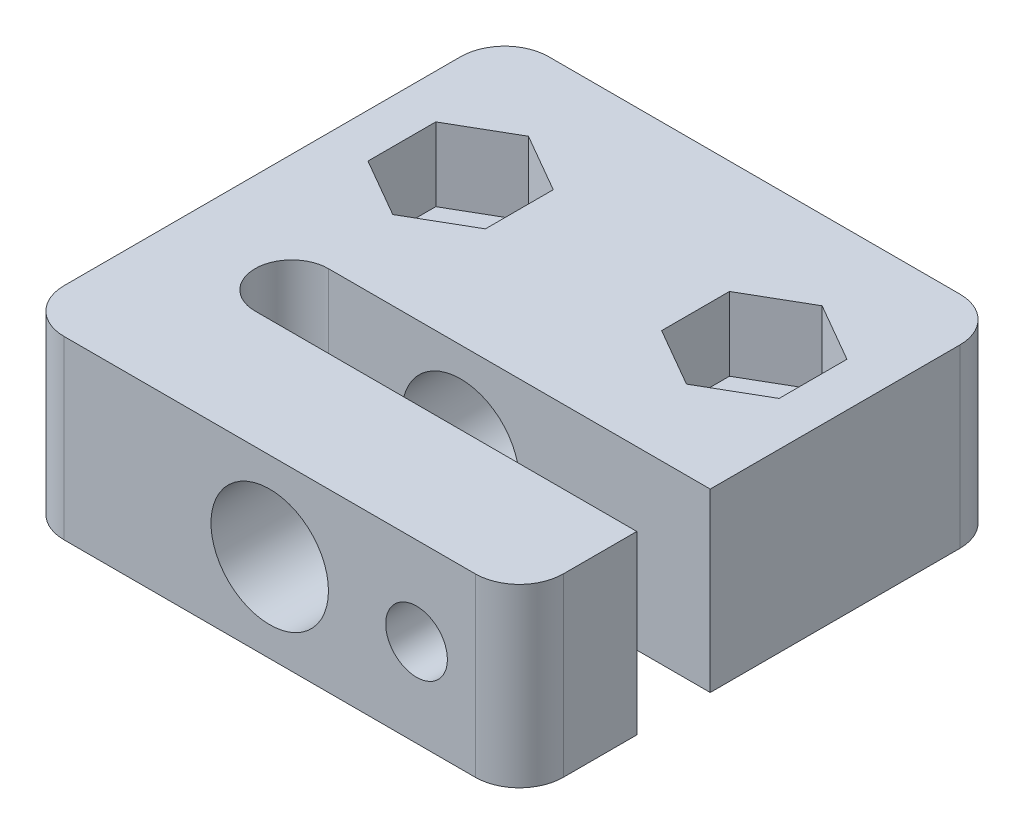
SolidWorks part; units mm, degrees
material "Delrin 2700 NC010, Low Viscosity Acetal Copolymer (SS)"
ref_plane "Front Plane" through (0, 0, 0) normal (0, 0, 1) x (1, 0, 0)
ref_plane "Top Plane" through (0, 0, 0) normal (0, 1, 0) x (1, 0, 0)
ref_plane "Right Plane" through (0, 0, 0) normal (1, 0, 0) x (0, 0, -1)
sketch "Sketch1" plane through (0, 0, 0) normal (0, 0, 1) x (1, 0, 0)
  line L1 (17, -6) -> (-17, -6)
  line L2 (17, -6) -> (17, 6)
  line L3 (17, 6) -> (-17, 6)
  line L4 (-17, -6) -> (-17, 6)
  line L5 (17, -6) -> (-17, 6) construction
  line L6 (17, 6) -> (-17, -6) construction
  point P0 (0, 0)
  dimension "D1" = 12
  dimension "D2" = 34
extrude "Boss-Extrude1" add sketch "Sketch1" along normal blind 33
sketch "Sketch2" plane through (0, 0, 33) normal (0, 0, 1) x (1, 0, 0)
  circle A0 centre (0, 0) radius 4
  dimension "D1" = 8
extrude "Cut-Extrude1" cut sketch "Sketch2" against normal through all
sketch "Sketch3" plane through (0, 6, 0) normal (0, 1, 0) x (1, 0, 0)
  line L0 (17, 0) -> (-17, 0) construction
  line L1 (0, -16.5) -> (0, 0) construction
  circle A0 centre (-10, -10) radius 2.55
  circle A1 centre (10, -10) radius 2.55
  dimension "D1" = 5.1
  dimension "D2" = 20
  dimension "D3" = 10
extrude "Cut-Extrude2" cut sketch "Sketch3" against normal through all
sketch "Sketch4" plane through (0, 6, 0) normal (0, 1, 0) x (1, 0, 0)
  line L0 (0, 0) -> (0, 6.2689) construction
  line L1 (-10, -5.3812) -> (-14, -7.6906)
  line L2 (-14, -7.6906) -> (-14, -12.3094)
  line L3 (-14, -12.3094) -> (-10, -14.6188)
  line L4 (-10, -14.6188) -> (-6, -12.3094)
  line L5 (-6, -12.3094) -> (-6, -7.6906)
  line L6 (-6, -7.6906) -> (-10, -5.3812)
  line L7 (6, -7.6906) -> (10, -5.3812)
  line L8 (6, -12.3094) -> (6, -7.6906)
  line L9 (10, -14.6188) -> (6, -12.3094)
  line L10 (14, -12.3094) -> (10, -14.6188)
  line L11 (14, -7.6906) -> (14, -12.3094)
  line L12 (10, -5.3812) -> (14, -7.6906)
  circle A0 centre (-10, -10) radius 4 construction
  circle A1 centre (10, -10) radius 4 construction
  dimension "D1" = 8
extrude "Cut-Extrude3" cut sketch "Sketch4" against normal blind 5
sketch "Sketch5" plane through (0, -6, 0) normal (0, -1, 0) x (1, 0, 0)
  circle A0 centre (10, 10) radius 4.5
  circle A1 centre (-10, 10) radius 4.5
  dimension "D1" = 9
extrude "Cut-Extrude4" cut sketch "Sketch5" against normal blind 2
sketch "Sketch6" plane through (0, 6, 0) normal (0, 1, 0) x (1, 0, 0)
  line L0 (17, -22.5) -> (-9, -22.5) construction
  line L1 (17, -33) -> (17, 0) construction
  line L2 (17, -25) -> (-9, -25)
  line L3 (17, -20) -> (-9, -20)
  line L4 (17, -33) -> (-17, -33) construction
  arc A0 (17, -25) -> (17, -20) centre (17, -22.5) ccw
  arc A1 (-9, -20) -> (-9, -25) centre (-9, -22.5) ccw
  point P4 (4, -22.5)
  dimension "D1" = 5
  dimension "D2" = 8
  dimension "D3" = 26
extrude "Cut-Extrude5" cut sketch "Sketch6" against normal through all
hole_wizard "M5x0.8 Tapped Hole1" positions "Sketch8" profile "Sketch7" tap size "M5x0.8" standard "ANSI Metric" end condition up to next
sketch "Sketch8" plane through (0, 0, 33) normal (0, 0, 1) x (1, 0, 0)
  line L0 (10, 0) -> (0, 0) construction
  point P0 (10, 0)
  dimension "D1" = 10
sketch "Sketch7" plane through (10, 0, 33) normal (1, 0, 0) x (0, -1, 0)
  line L0 (0, 0) -> (0, 8)
  line L1 (0, 8) -> (2.1, 8)
  line L2 (2.1, 8) -> (2.1, 0)
  line L5 (2.1, 0) -> (0, 0)
  line L11 (0, -6.35) -> (0, 107.95) construction
  dimension "Thread Major Dia." = 4.2
  dimension "Thru Tap Drill Depth" = 8
fillet "Fillet1" radius 3 4 edges at (-17, 0, 0) (17, 0, 0) (17, 0, 33) (-17, 0, 33)
